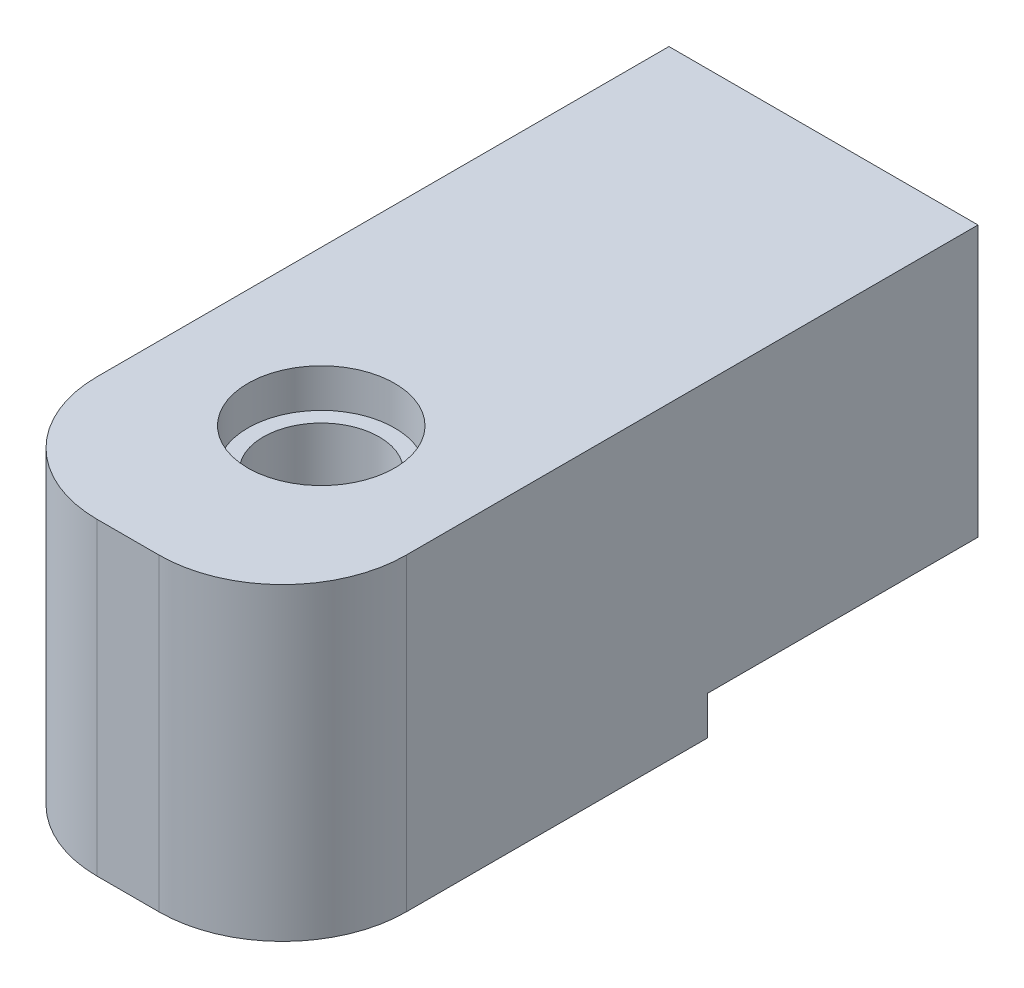
SolidWorks part; units mm, degrees
material "1023 Carbon Steel Sheet (SS)"
ref_plane "Front Plane" through (0, 0, 0) normal (0, 0, 1) x (1, 0, 0)
ref_plane "Top Plane" through (0, 0, 0) normal (0, 1, 0) x (1, 0, 0)
ref_plane "Right Plane" through (0, 0, 0) normal (1, 0, 0) x (0, 0, -1)
sketch "Sketch1" plane through (0, 0, 0) normal (0, 0, 1) x (1, 0, 0)
  line L1 (-12.7, 12.7) -> (12.7, 12.7)
  line L2 (-12.7, 12.7) -> (-12.7, -12.7)
  line L3 (-12.7, -12.7) -> (12.7, -12.7)
  line L4 (12.7, 12.7) -> (12.7, -12.7)
  line L5 (-12.7, 12.7) -> (12.7, -12.7) construction
  line L6 (-12.7, -12.7) -> (12.7, 12.7) construction
  point P0 (0, 0)
  dimension "D1" = 25.4
extrude "Boss-Extrude1" add sketch "Sketch1" along normal blind 57.15
fillet "Fillet2" radius 10.16 2 edges at (-12.7, 0, 57.15) (12.7, 0, 57.15)
sketch "Sketch2" plane through (0, -12.7, 0) normal (0, -1, 0) x (1, 0, 0)
  line L0 (-12.7, 0) -> (12.7, 0) construction
  line L1 (-12.7, 0) -> (12.7, 0)
  line L2 (-12.7, 0) -> (-12.7, 22.225)
  line L3 (-12.7, 22.225) -> (12.7, 22.225)
  line L4 (12.7, 0) -> (12.7, 22.225)
  line L5 (12.7, 46.99) -> (12.7, 0) construction
  line L6 (-12.7, 46.99) -> (-12.7, 0) construction
  dimension "D1" = 0
  dimension "D2" = 22.225
  dimension "D3" = 0
  dimension "D4" = 0
extrude "Cut-Extrude2" cut sketch "Sketch2" against normal blind 3.175
sketch "Sketch3" plane through (0, -12.7, 0) normal (0, -1, 0) x (1, 0, 0)
  circle A0 centre (0, 41.275) radius 4.7625
  dimension "D1" = 9.525
  dimension "D2" = 41.275
extrude "Cut-Extrude3" cut sketch "Sketch3" against normal blind 22.225
sketch "Sketch4" plane through (0, 12.7, 0) normal (0, 1, 0) x (1, 0, 0)
  line L0 (12.7, 0) -> (-12.7, 0) construction
  circle A0 centre (0, -41.275) radius 6.0325
  dimension "D1" = 12.065
  dimension "D2" = 41.275
extrude "Cut-Extrude4" cut sketch "Sketch4" against normal blind 3.175
sketch "Sketch5" plane through (0, 0, 0) normal (0, 0, -1) x (-1, 0, 0)
  circle A0 centre (0, 0) radius 6.35
  dimension "D1" = 12.7
extrude "Cut-Extrude5" cut sketch "Sketch5" against normal blind 30.1752
